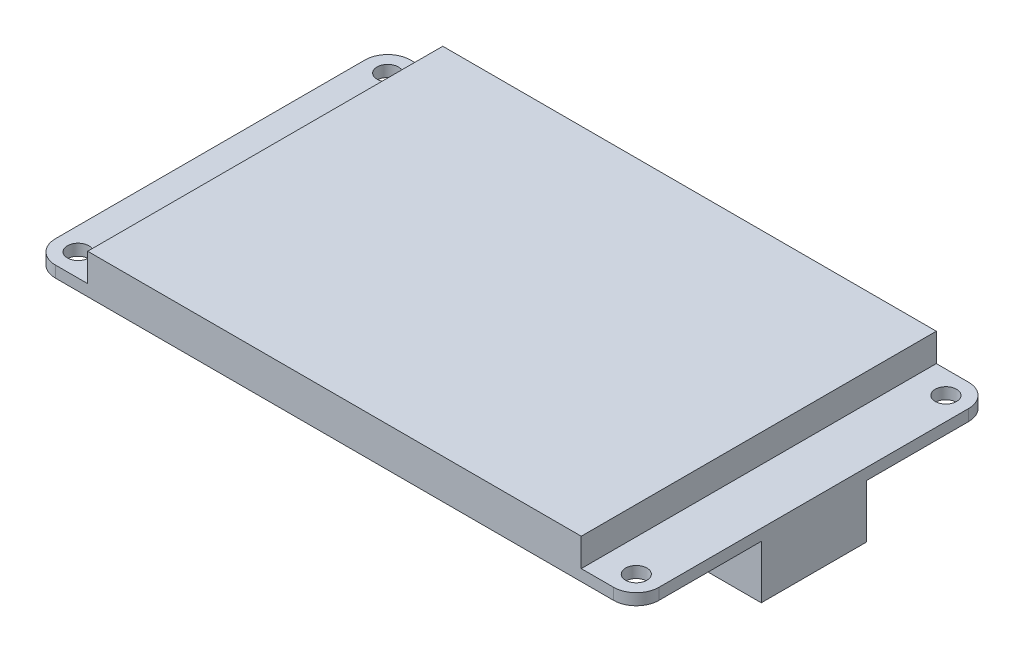
SolidWorks part; units mm, degrees
ref_plane "Front Plane" through (0, 0, 0) normal (0, 0, 1) x (1, 0, 0)
ref_plane "Top Plane" through (0, 0, 0) normal (0, 1, 0) x (1, 0, 0)
ref_plane "Right Plane" through (0, 0, 0) normal (1, 0, 0) x (0, 0, -1)
sketch "Sketch1" plane through (0, 0, 0) normal (0, 1, 0) x (1, 0, 0)
  line L1 (0, 0) -> (85, 0)
  line L2 (0, 0) -> (0, 50)
  line L3 (0, 50) -> (85, 50)
  line L4 (85, 0) -> (85, 50)
  dimension "D1" = 85
  dimension "D2" = 50
extrude "Boss-Extrude1" add sketch "Sketch1" along normal blind 5.55
sketch "Sketch2" plane through (0, 5.55, 0) normal (0, 1, 0) x (1, 0, 0)
  line L0 (85, 50) -> (0, 50) construction
  line L1 (7.75, 50) -> (77.25, 50) construction
  line L2 (7.75, 50) -> (7.75, 0) construction
  line L3 (7.75, 0) -> (77.25, 0) construction
  line L4 (77.25, 50) -> (77.25, 0) construction
  line L5 (0, 0) -> (85, 0) construction
  line L7 (0, 50) -> (7.75, 50)
  line L8 (0, 50) -> (0, 0)
  line L9 (0, 0) -> (7.75, 0)
  line L10 (7.75, 50) -> (7.75, 0)
  line L11 (77.25, 50) -> (85, 50)
  line L12 (77.25, 50) -> (77.25, 0)
  line L13 (77.25, 0) -> (85, 0)
  line L14 (85, 50) -> (85, 0)
  point P8 (42.5, 0)
  dimension "D1" = 69.5
extrude "Cut-Extrude1" cut sketch "Sketch2" against normal offset from surface (3.95 mm away) 1.6 up to face at (42.5, 0, -25)
sketch "Sketch3" plane through (0, 1.6, 0) normal (0, 1, 0) x (1, 0, 0)
  line L0 (1.7, 46.8) -> (1.7, 48.3) construction
  line L5 (1.7, 48.3) -> (3.2, 48.3) construction
  line L6 (0, 50) -> (0, 0) construction
  line L7 (7.75, 50) -> (0, 50) construction
  line L8 (0, 46.8) -> (0, 50)
  line L9 (0, 50) -> (3.2, 50)
  line L10 (42.5, 50) -> (42.5, 25) construction
  line L11 (77.25, 50) -> (7.75, 50) construction
  line L12 (42.5, 25) -> (0, 25) construction
  line L13 (1.7, 1.7) -> (3.2, 1.7) construction
  line L14 (1.7, 3.2) -> (1.7, 1.7) construction
  line L15 (0, 0) -> (3.2, 0)
  line L16 (0, 3.2) -> (0, 0)
  line L17 (83.3, 3.2) -> (83.3, 1.7) construction
  line L18 (83.3, 1.7) -> (81.8, 1.7) construction
  line L19 (83.3, 48.3) -> (81.8, 48.3) construction
  line L20 (83.3, 46.8) -> (83.3, 48.3) construction
  line L21 (85, 3.2) -> (85, 0)
  line L22 (85, 0) -> (81.8, 0)
  line L23 (85, 50) -> (81.8, 50)
  line L24 (85, 46.8) -> (85, 50)
  circle A0 centre (3.2, 46.8) radius 1.5
  arc A1 (3.2, 50) -> (0, 46.8) centre (3.2, 46.8) ccw
  arc A2 (3.2, 0) -> (0, 3.2) centre (3.2, 3.2) cw
  circle A3 centre (3.2, 3.2) radius 1.5
  circle A4 centre (81.8, 3.2) radius 1.5
  arc A5 (81.8, 0) -> (85, 3.2) centre (81.8, 3.2) ccw
  arc A6 (81.8, 50) -> (85, 46.8) centre (81.8, 46.8) cw
  circle A7 centre (81.8, 46.8) radius 1.5
  dimension "D1" = 3
  dimension "D2" = 1.7
  dimension "D3" = 1.7
extrude "Cut-Extrude2" cut sketch "Sketch3" against normal through all
sketch "Sketch4" plane through (0, 0, 0) normal (0, -1, 0) x (1, 0, 0)
  line L1 (31.0087, -3.3294) -> (36.7091, -3.3294)
  line L2 (31.0087, -3.3294) -> (31.0087, -20.4306)
  line L3 (31.0087, -20.4306) -> (36.7091, -20.4306)
  line L4 (36.7091, -3.3294) -> (36.7091, -20.4306)
extrude "Boss-Extrude2" add sketch "Sketch4" along normal blind 3
sketch "Sketch5" plane through (0, 0, 0) normal (0, -1, 0) x (1, 0, 0)
  line L0 (85, -3.2) -> (85, -46.8) construction
  line L1 (85, -32.4) -> (76.5, -32.4)
  line L2 (85, -32.4) -> (85, -17.6)
  line L3 (85, -17.6) -> (76.5, -17.6)
  line L4 (76.5, -32.4) -> (76.5, -17.6)
  line L5 (3.2, 0) -> (81.8, 0) construction
  point P8 (85, -25)
  dimension "D1" = 17.6
  dimension "D2" = 8.5
extrude "Boss-Extrude3" add sketch "Sketch5" along normal blind 7.5
